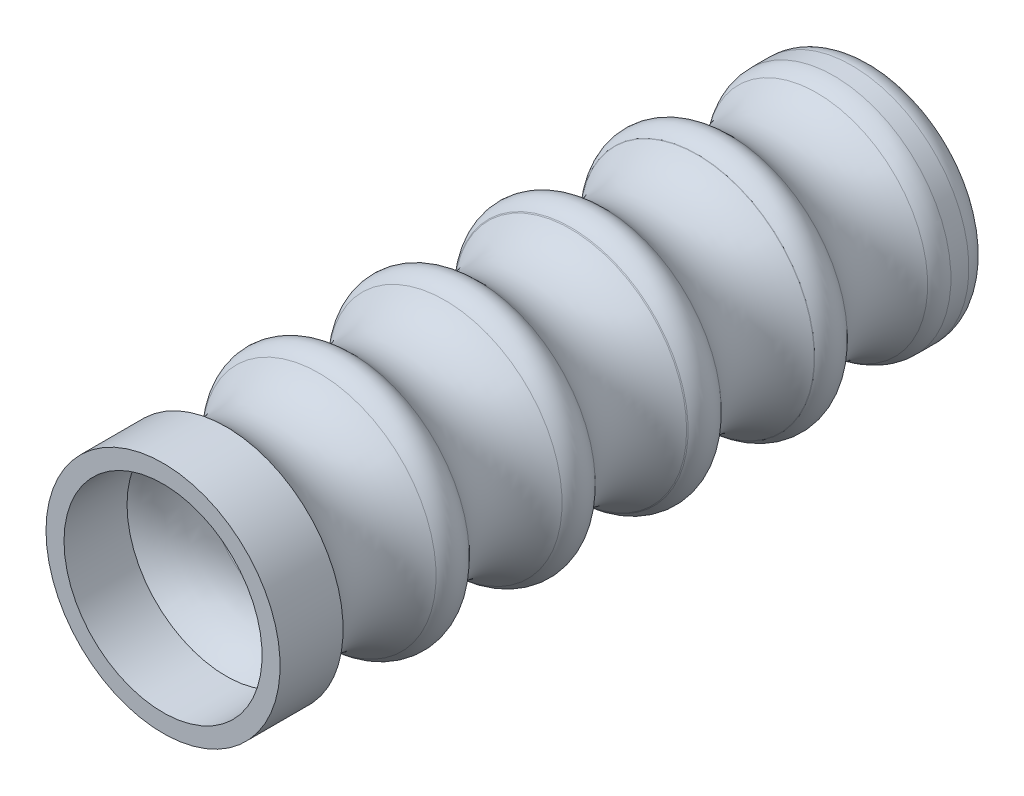
SolidWorks part; units mm, degrees
material "ABS"
ref_plane "Plano frontal" through (0, 0, 0) normal (0, 0, 1) x (1, 0, 0)
ref_plane "Plano superior" through (0, 0, 0) normal (0, 1, 0) x (1, 0, 0)
ref_plane "Plano direito" through (0, 0, 0) normal (1, 0, 0) x (0, 0, -1)
sketch "Esboço2" plane through (0, 0, 0) normal (0, 1, 0) x (1, 0, 0)
  line L0 (-55, 0) -> (55, 0) construction
  line L1 (8.5561, 33.1613) -> (8.5561, 47.1613) construction
  line L2 (8.5561, -12.1613) -> (6.5561, -12.1613)
  line L3 (-4.4439, 38.8369) -> (-4.4439, -28.5039) construction
  line L4 (6.0561, 66.8387) -> (4.6238, 66.8387)
  line L5 (6.5561, -12.1613) -> (6.5561, -5.1613)
  line L6 (8.5561, 47.1613) -> (8.5561, 61.1613) construction
  line L7 (8.5561, 64.3387) -> (8.5561, 62.3456)
  line L8 (8.5561, -5.1613) -> (8.5561, -12.1613)
  line L9 (8.5588, 33.1545) -> (8.4678, 33.079)
  line L10 (8.5561, 47.1613) -> (8.5882, 47.182)
  line L11 (4.6238, 1.8387) -> (4.6238, 66.8387)
  arc A0 (8.4678, 33.079) -> (8.5561, 22.8387) centre (13.2849, 28) ccw
  arc A1 (8.5588, 19.1545) -> (8.5588, 8.8455) centre (13.295, 14) ccw
  arc A2 (8.5561, 5.1613) -> (8.5561, -5.1613) centre (13.2849, 0) ccw
  arc A3 (8.5561, 5.1613) -> (8.5588, 8.8455) centre (6.8673, 7.0046) ccw
  arc A4 (8.5588, 19.1545) -> (8.5561, 22.8387) centre (6.8673, 20.9954) ccw
  arc A5 (8.5561, 64.3387) -> (6.0561, 66.8387) centre (6.0561, 64.3387) ccw
  arc A6 (8.5561, 47.1613) -> (8.5561, 36.8387) centre (13.2849, 42) ccw
  arc A7 (8.5588, 33.1545) -> (8.5561, 36.8387) centre (6.8673, 34.9954) ccw
  arc A8 (7.8747, 60.4419) -> (8.5561, 50.8387) centre (13.2849, 56) ccw
  arc A9 (8.5882, 47.182) -> (8.5561, 50.8387) centre (6.8673, 48.9954) ccw
  arc A10 (7.8747, 60.4419) -> (8.5561, 62.3456) centre (5.5561, 62.3456) ccw
  spline S0 degree 2 poles (6.5561, -5.1613) (3.76, -2.1379) (4.6238, 1.8387) knots 0 0 0 1 1 1
  point P0 (13.2849, 28)
  point P1 (13.295, 14)
  point P21 (13.2899, 21)
  point P44 (8.5561, 61.1613)
  dimension "D2" = 2.5
  dimension "D4" = 2.5
  dimension "D10" = 3
  dimension "D1" = 14
  dimension "D3" = 13
  dimension "D5" = 2
  dimension "D6" = 2
  dimension "D7" = 14
  dimension "D9" = 14
  dimension "D8" = 2
revolve "Revolução1" add sketch "Esboço2" angle 360 about L3
